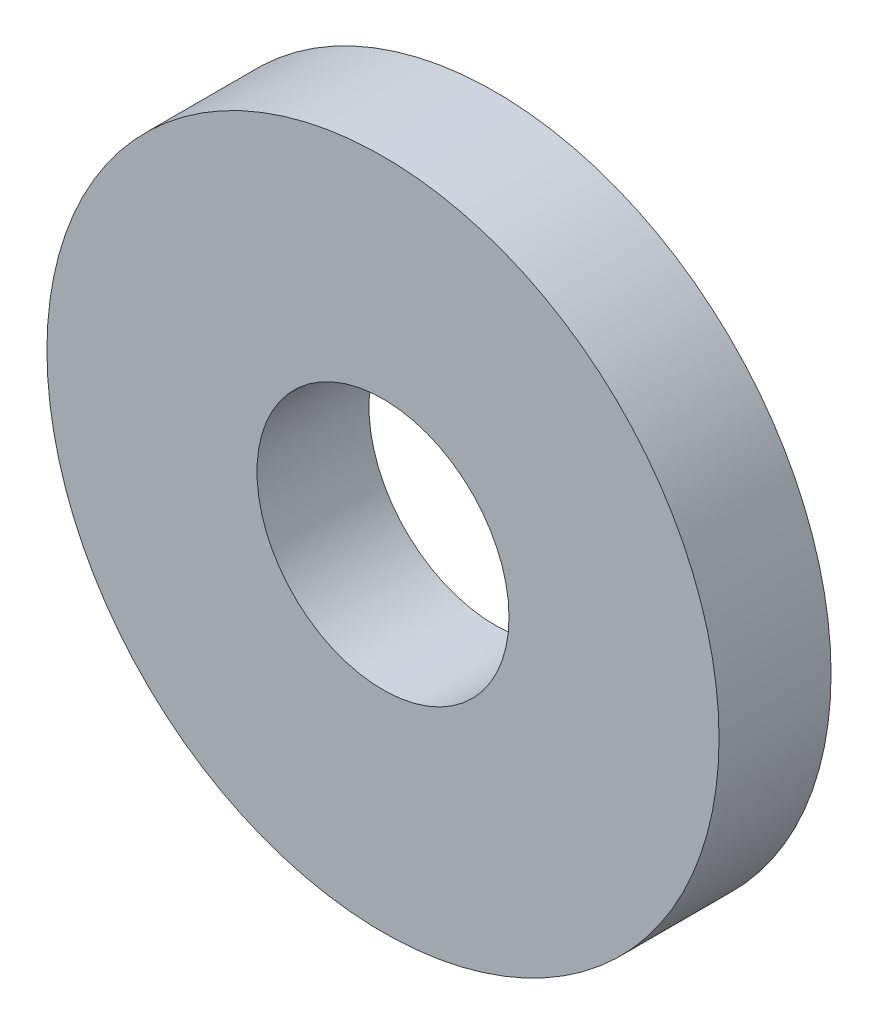
SolidWorks part; units mm, degrees
ref_plane "Front Plane" through (0, 0, 0) normal (0, 0, 1) x (1, 0, 0)
ref_plane "Top Plane" through (0, 0, 0) normal (0, 1, 0) x (1, 0, 0)
ref_plane "Right Plane" through (0, 0, 0) normal (1, 0, 0) x (0, 0, -1)
sketch "Sketch1" plane through (0, 0, 0) normal (0, 0, 1) x (1, 0, 0)
  circle A0 centre (0, 0) radius 2.25
  circle A1 centre (0, 0) radius 6
  dimension "D1" = 4.5
  dimension "D2" = 12
extrude "Boss-Extrude1" add sketch "Sketch1" along normal blind 2
